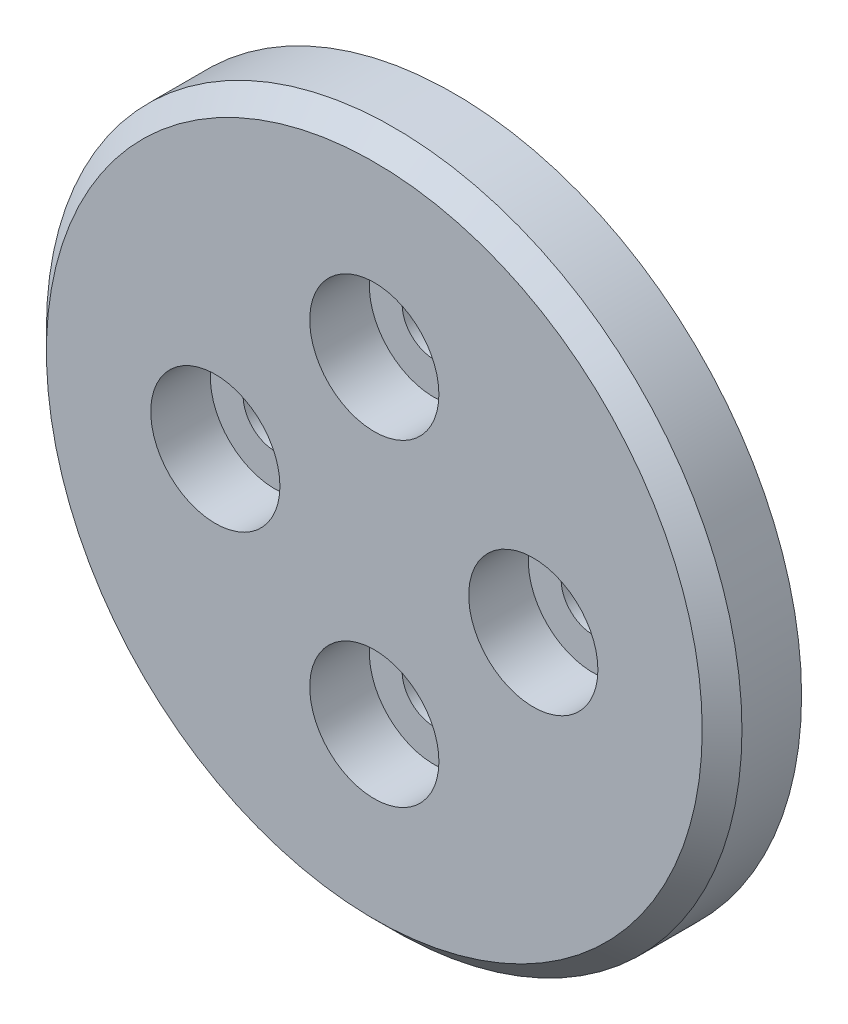
SolidWorks part; units mm, degrees
ref_plane "Front Plane" through (0, 0, 0) normal (0, 0, 1) x (1, 0, 0)
ref_plane "Top Plane" through (0, 0, 0) normal (0, 1, 0) x (1, 0, 0)
ref_plane "Right Plane" through (0, 0, 0) normal (1, 0, 0) x (0, 0, -1)
sketch "Sketch1" plane through (0, 0, 0) normal (0, 0, 1) x (1, 0, 0)
  circle A0 centre (0, 0) radius 17.5
  dimension "D1" = 35
extrude "Boss-Extrude1" add sketch "Sketch1" along normal blind 4
sketch "Sketch2" plane through (0, 0, 0) normal (0, 0, -1) x (-1, 0, 0)
  circle A0 centre (0, 0) radius 12
  dimension "D1" = 24
extrude "Boss-Extrude2" add sketch "Sketch2" along normal blind 0.6
hole_wizard "CBORE for M3 SHCS1" positions "Sketch3" profile "Sketch4" counterbore size "M3" standard "ANSI Metric" end condition through all
sketch "Sketch3" plane through (0, 0, 4) normal (0, 0, 1) x (1, 0, 0)
  line L0 (0, 8) -> (0, 0) construction
  point P0 (0, 8)
  point P12 (8, 0)
  point P13 (0, -8)
  point P14 (-8, 0)
  dimension "D1" = 8
  dimension "D2" = 4
sketch "Sketch4" plane through (0, 8, 4) normal (1, 0, 0) x (0, -1, 0)
  line L0 (0, 0) -> (0, 4.6)
  line L1 (0, 4.6) -> (1.6, 4.6)
  line L3 (1.6, 4.6) -> (1.6, 3)
  line L4 (1.6, 3) -> (3.25, 3)
  line L5 (3.25, 3) -> (3.25, 0)
  line L7 (3.25, 0) -> (0, 0)
  line L11 (0, -6.35) -> (0, 107.95) construction
  dimension "Thru Hole Dia." = 3.2
  dimension "Thru Hole Depth" = 4.6
  dimension "C'Bore Dia." = 6.5
  dimension "C'Bore Depth" = 3
chamfer "Chamfer1" distance 1 angle 45 1 edges at (17.5, 0, 4)
